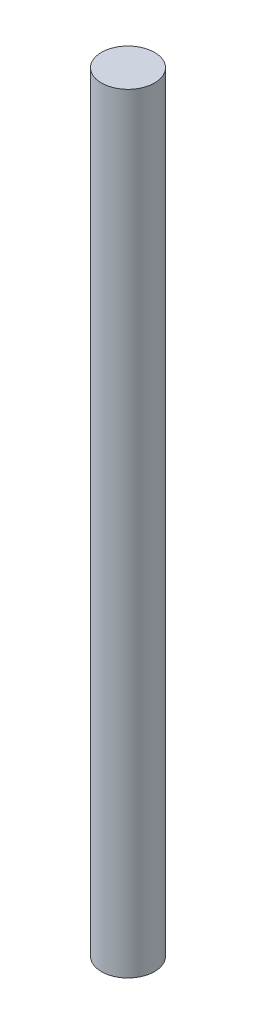
SolidWorks part; units mm, degrees
ref_plane "Front Plane" through (0, 0, 0) normal (0, 0, 1) x (1, 0, 0)
ref_plane "Top Plane" through (0, 0, 0) normal (0, 1, 0) x (1, 0, 0)
ref_plane "Right Plane" through (0, 0, 0) normal (1, 0, 0) x (0, 0, -1)
sketch "Sketch1" plane through (0, 0, 0) normal (0, 1, 0) x (1, 0, 0)
  circle A0 centre (0, 0) radius 6.35
extrude "Boss-Extrude1" add sketch "Sketch1" along normal blind 184.15
